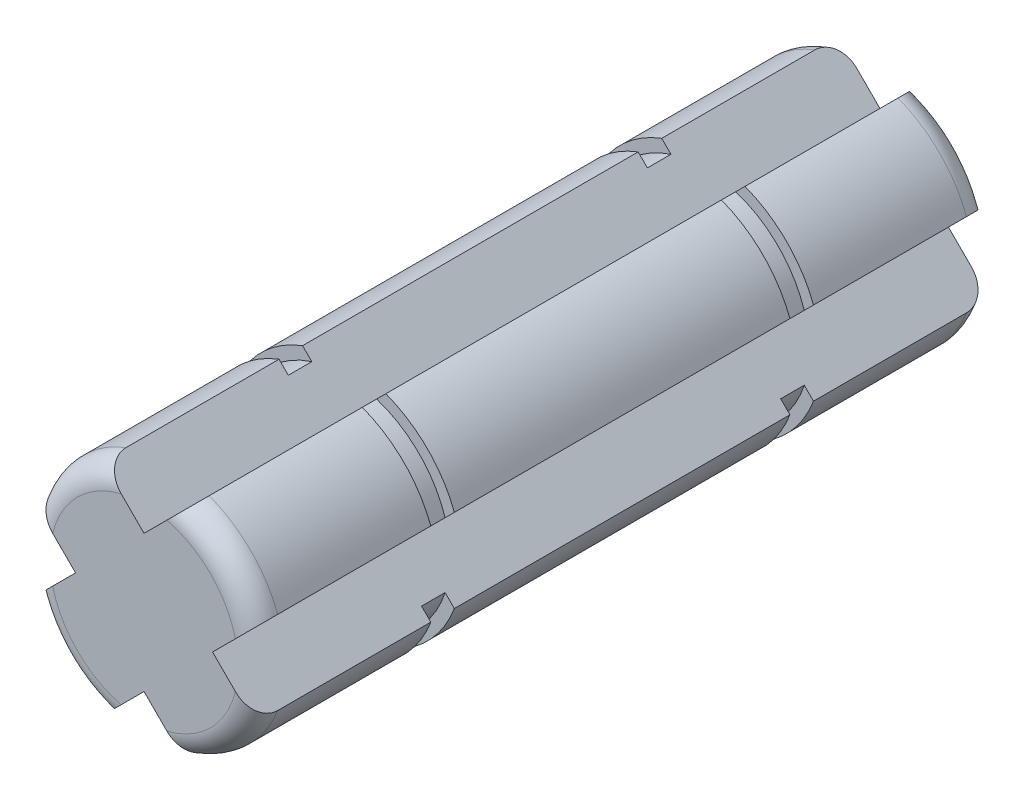
SolidWorks part; units mm, degrees
material "ABS"
ref_plane "Front Plane" through (0, 0, 0) normal (0, 0, 1) x (1, 0, 0)
ref_plane "Top Plane" through (0, 0, 0) normal (0, 1, 0) x (1, 0, 0)
ref_plane "Right Plane" through (0, 0, 0) normal (1, 0, 0) x (0, 0, -1)
sketch "Sketch1" plane through (0, 0, 0) normal (0, 0, 1) x (1, 0, 0)
  line L0 (0, 1.4779) -> (0, -1.4779) construction
  line L1 (-0.898, 2.376) -> (0, 1.4779)
  line L2 (0, 1.4779) -> (0.898, 2.376)
  line L3 (2.376, 0.898) -> (1.4779, 0)
  line L4 (1.4779, 0) -> (2.376, -0.898)
  line L5 (0.898, -2.376) -> (0, -1.4779)
  line L6 (0, -1.4779) -> (-0.898, -2.376)
  line L7 (-2.376, -0.898) -> (-1.4779, 0)
  line L8 (-1.4779, 0) -> (-2.376, 0.898)
  arc A0 (-2.376, -0.898) -> (-0.898, -2.376) centre (0, 0) ccw
  arc A1 (-0.898, 2.376) -> (-2.376, 0.898) centre (0, 0) ccw
  arc A2 (2.376, 0.898) -> (0.898, 2.376) centre (0, 0) ccw
  arc A3 (0.898, -2.376) -> (2.376, -0.898) centre (0, 0) ccw
  point P20 (0, 0)
  dimension "D1" = 5.08
  dimension "D2" = 90
  dimension "D3" = 1.27
  dimension "D4" = 1.27
  dimension "D5" = 4
extrude "Boss-Extrude1" add sketch "Sketch1" along normal mid plane 15.875
sketch "Sketch2" plane through (0, 0, 0) normal (1, 0, 0) x (0, 0, -1)
  line L3 (-4.1275, 2.54) -> (-4.1275, 2.286)
  line L4 (-4.1275, 2.286) -> (-3.6195, 2.286)
  line L7 (0, 0) -> (-8.0587, 0) construction
  line L8 (-3.6195, 2.286) -> (-3.6195, 2.54)
  line L9 (-3.6195, 2.54) -> (-4.1275, 2.54)
  dimension "D3" = 0.508
  dimension "D4" = 0.254
revolve "Cut-Revolve2" cut sketch "Sketch2" angle 360 about L7
mirror "Mirror1" about plane through (0, 0, 0) normal (0, 0, 1) of "Cut-Revolve2"
fillet "Fillet3" radius 0.508 8 edges at (1.7961, -1.7961, -7.9375) (-1.7961, -1.7961, -7.9375) (1.7961, 1.7961, -7.9375) (-1.7961, 1.7961, -7.9375) (-1.7961, 1.7961, 7.9375) (-1.7961, -1.7961, 7.9375) (1.7961, -1.7961, 7.9375) (1.7961, 1.7961, 7.9375)
